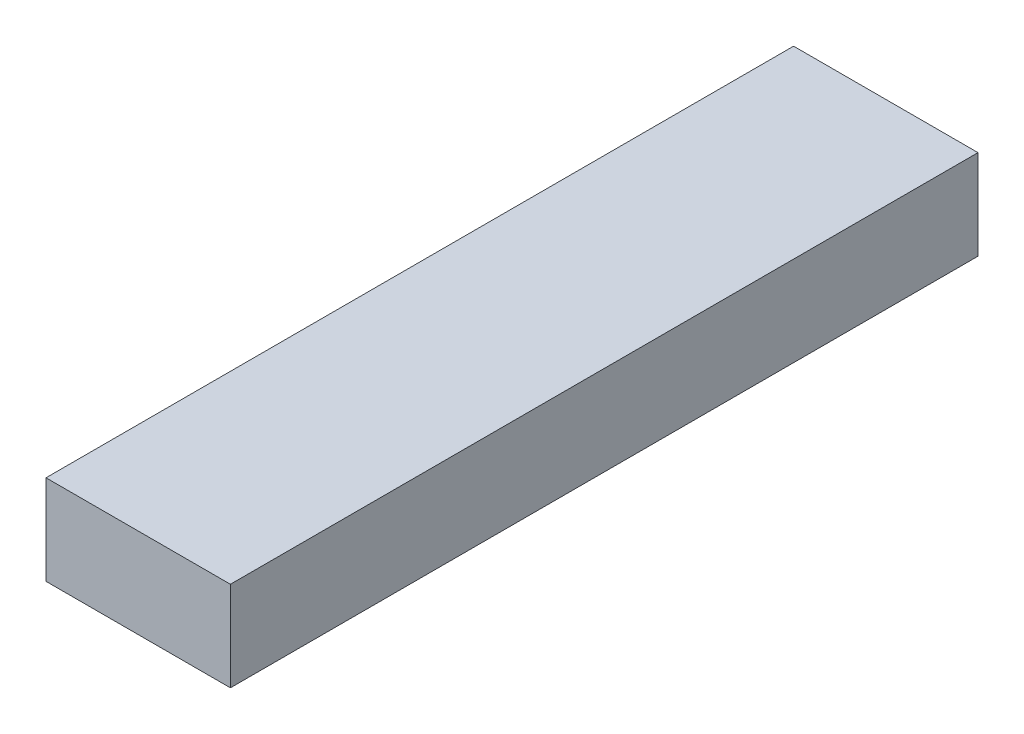
SolidWorks part; units mm, degrees
ref_plane "Front Plane" through (0, 0, 0) normal (0, 0, 1) x (1, 0, 0)
ref_plane "Top Plane" through (0, 0, 0) normal (0, 1, 0) x (1, 0, 0)
ref_plane "Right Plane" through (0, 0, 0) normal (1, 0, 0) x (0, 0, -1)
sketch "Sketch1" plane through (0, 0, 0) normal (0, 0, 1) x (1, 0, 0)
  line L1 (-1.85, -0.9) -> (1.85, -0.9)
  line L2 (-1.85, -0.9) -> (-1.85, 0.9)
  line L3 (-1.85, 0.9) -> (1.85, 0.9)
  line L4 (1.85, -0.9) -> (1.85, 0.9)
  line L5 (-1.85, -0.9) -> (1.85, 0.9) construction
  line L6 (-1.85, 0.9) -> (1.85, -0.9) construction
  point P0 (0, 0)
  dimension "D1" = 3.7
  dimension "D2" = 1.8
extrude "Boss-Extrude1" add sketch "Sketch1" along normal blind 15
